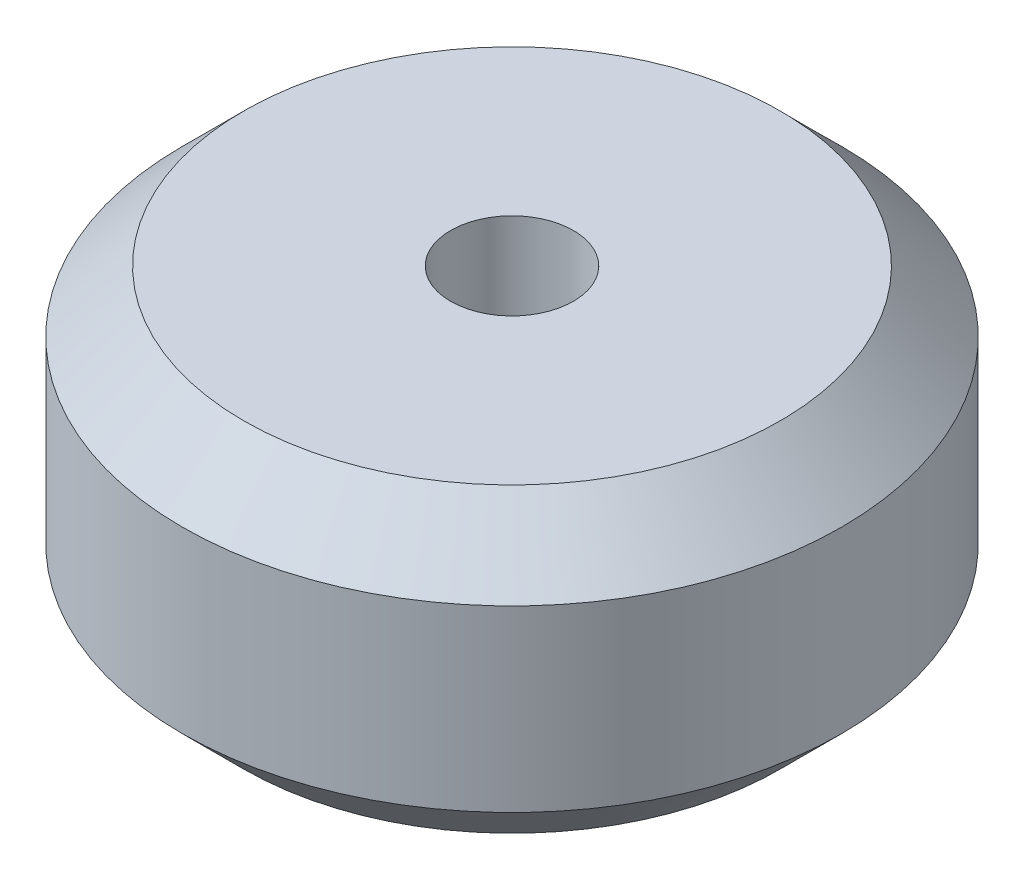
SolidWorks part; units mm, degrees
ref_plane "Front Plane" through (0, 0, 0) normal (0, 0, 1) x (1, 0, 0)
ref_plane "Top Plane" through (0, 0, 0) normal (0, 1, 0) x (1, 0, 0)
ref_plane "Right Plane" through (0, 0, 0) normal (1, 0, 0) x (0, 0, -1)
sketch "Sketch1" plane through (0, 0, 0) normal (0, 1, 0) x (1, 0, 0)
  circle A0 centre (0, 0) radius 11.938
  circle A1 centre (0, 0) radius 2.2225
  dimension "D1" = 23.876
  dimension "D2" = 4.445
extrude "Boss-Extrude1" add sketch "Sketch1" along normal blind 10.922
chamfer "Chamfer1" distance 2.2225 angle 45 2 edges at (0, 0, 11.938) (0, 10.922, 11.938)
